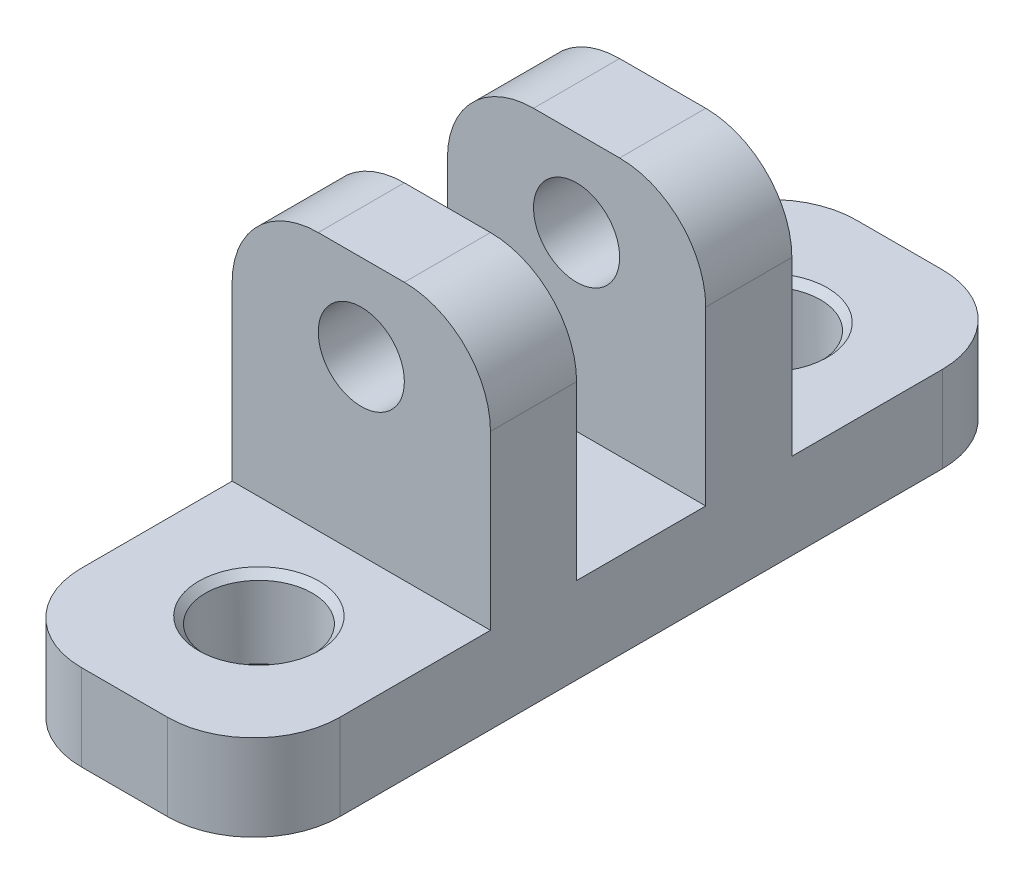
SolidWorks part; units mm, degrees
material "6061-T6 (SS)"
ref_plane "Front Plane" through (0, 0, 0) normal (0, 0, 1) x (1, 0, 0)
ref_plane "Top Plane" through (0, 0, 0) normal (0, 1, 0) x (1, 0, 0)
ref_plane "Right Plane" through (0, 0, 0) normal (1, 0, 0) x (0, 0, -1)
sketch "Sketch1" plane through (0, 0, 0) normal (0, 1, 0) x (1, 0, 0)
  line L0 (60.325, 0) -> (0, 0) construction
  line L1 (60.325, 28.575) -> (79.375, 28.575)
  line L2 (60.325, 28.575) -> (60.325, -28.575)
  line L3 (60.325, -28.575) -> (79.375, -28.575)
  line L4 (79.375, 28.575) -> (79.375, -28.575)
  circle A0 centre (0, 0) radius 72.39 construction
  dimension "D1" = 144.78
  dimension "D2" = 19.05
  dimension "D3" = 57.15
  dimension "D4" = 60.325
extrude "Boss-Extrude1" add sketch "Sketch1" along normal blind 25.4
sketch "Sketch2" plane through (79.375, 0, 0) normal (1, 0, 0) x (0, 0, -1)
  line L0 (-28.575, 25.4) -> (28.575, 25.4) construction
  line L1 (-28.575, 25.4) -> (-11.1125, 25.4)
  line L2 (-28.575, 25.4) -> (-28.575, 6.35)
  line L3 (-28.575, 6.35) -> (-11.1125, 6.35)
  line L4 (-11.1125, 25.4) -> (-11.1125, 6.35)
  line L5 (-4.7625, 25.4) -> (4.7625, 25.4)
  line L6 (-4.7625, 25.4) -> (-4.7625, 6.35)
  line L7 (-4.7625, 6.35) -> (4.7625, 6.35)
  line L8 (4.7625, 25.4) -> (4.7625, 6.35)
  line L10 (28.575, 25.4) -> (11.1125, 25.4)
  line L11 (28.575, 25.4) -> (28.575, 6.35)
  line L12 (28.575, 6.35) -> (11.1125, 6.35)
  line L13 (11.1125, 25.4) -> (11.1125, 6.35)
  line L14 (-28.575, 0) -> (28.575, 0) construction
  line L16 (0, 25.4) -> (0, 6.35) construction
  dimension "D1" = 6.35
  dimension "D2" = 9.525
  dimension "D3" = 6.35
extrude "Cut-Extrude1" cut sketch "Sketch2" against normal through all
ref_plane "Plane1" through (0, 0, 0) normal (0, 0, 1) x (1, 0, 0)
sketch "Sketch9" plane through (0, 0, 11.1125) normal (0, 0, 1) x (1, 0, 0)
  line L0 (60.325, 25.4) -> (79.375, 25.4) construction
  line L2 (69.85, 19.05) -> (69.85, 25.4) construction
  circle A0 centre (69.85, 19.05) radius 3.175
  dimension "D1" = 6.35
  dimension "D2" = 6.35
extrude "Cut-Extrude3" cut sketch "Sketch9" against normal through all
fillet "Fillet1" radius 6.35 8 edges at (60.325, 3.175, -28.575) (79.375, 3.175, -28.575) (60.325, 3.175, 28.575) (79.375, 3.175, 28.575) (79.375, 25.4, -7.9375) (60.325, 25.4, -7.9375) (60.325, 25.4, 7.9375) (79.375, 25.4, 7.9375)
hole_wizard "Hole1" positions "Sketch10" profile "Sketch11" legacy end condition through all
sketch "Sketch10" plane through (0, 6.35, 0) normal (0, 1, 0) x (1, 0, 0)
  line L0 (0, 0) -> (72.39, 0) construction
  line L2 (0, 0) -> (69.9234, 18.7359)
  line L4 (0, 0) -> (69.9234, -18.7359)
  line L6 (72.39, 0) -> (79.375, 0)
  line L7 (79.375, -4.7625) -> (79.375, 4.7625) construction
  circle A0 centre (0, 0) radius 72.39
  point P10 (69.9234, 18.7359)
  point P15 (69.9234, -18.7359)
  dimension "D1" = 144.78
  dimension "D2" = 30
  dimension "D3" = 15
sketch "Sketch11" plane through (69.9234, 6.35, -18.7359) normal (1, 0, 0) x (0, 0, 1)
  line L0 (0, 0) -> (0, 6.35)
  line L1 (0, 6.35) -> (3.937, 6.35)
  line L2 (3.937, 6.35) -> (3.937, 0)
  line L5 (3.937, 0) -> (0, 0)
  line L11 (0, -6.35) -> (0, 107.95) construction
  dimension "Thru Hole Dia." = 7.874
  dimension "Thru Hole Depth" = 6.35
chamfer "Chamfer1" distance 0.508 angle 45 4 edges at (69.9234, 6.35, -14.7989) (69.9234, 0, -14.7989) (69.9234, 6.35, 22.6729) (69.9234, 0, 22.6729)
equation "\"D3@Sketch10\"=\"D2@Sketch10\"/2"
